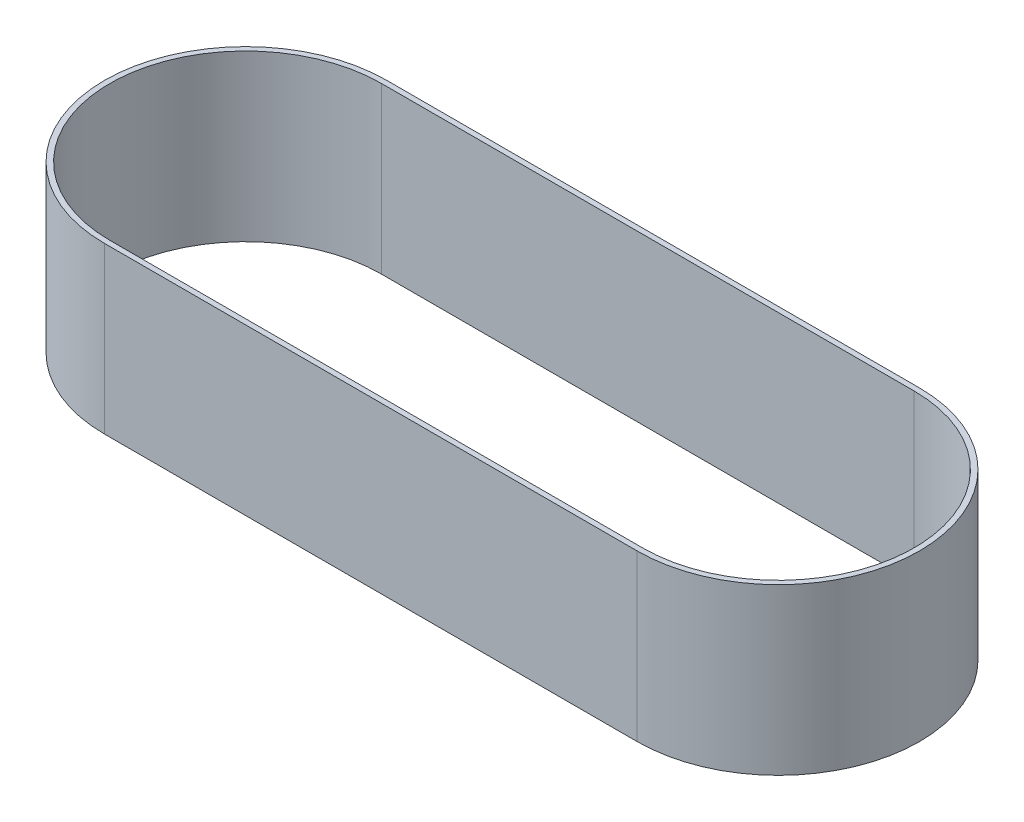
SolidWorks part; units mm, degrees
ref_plane "Front Plane" through (0, 0, 0) normal (0, 0, 1) x (1, 0, 0)
ref_plane "Top Plane" through (0, 0, 0) normal (0, 1, 0) x (1, 0, 0)
ref_plane "Right Plane" through (0, 0, 0) normal (1, 0, 0) x (0, 0, -1)
sketch "Sketch1" plane through (0, 0, 0) normal (0, 1, 0) x (1, 0, 0)
  line L0 (-100, 51) -> (100, 51)
  line L1 (-100, -53) -> (100, -53)
  line L3 (-100, 53) -> (100, 53)
  line L5 (-100, -53) -> (100, 53) construction
  line L6 (-100, 53) -> (100, -53) construction
  line L7 (-100, -51) -> (100, -51)
  arc A0 (-100, 53) -> (-100, -53) centre (-100, 0) ccw
  arc A1 (100, -53) -> (100, 53) centre (100, 0) ccw
  arc A2 (100, -51) -> (100, 51) centre (100, 0) ccw
  arc A3 (-100, 51) -> (-100, -51) centre (-100, 0) ccw
  point P0 (0, 0)
  point P14 (0, 0)
  point P15 (0, 0)
  dimension "D1" = 200
  dimension "D2" = 106
  dimension "D4" = 200
  dimension "D3" = 2
extrude "Boss-Extrude1" add sketch "Sketch1" along normal blind 62
